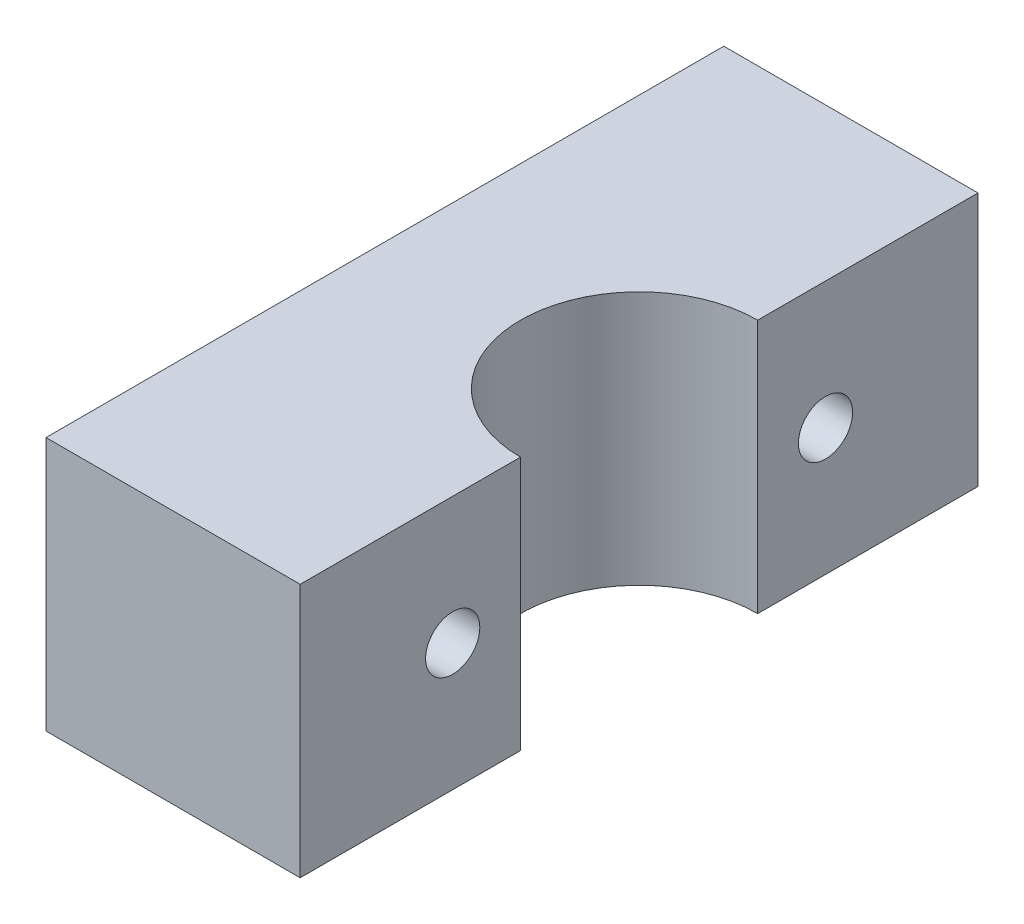
SolidWorks part; units mm, degrees
ref_plane "Спереди" through (0, 0, 0) normal (0, 0, 1) x (1, 0, 0)
ref_plane "Сверху" through (0, 0, 0) normal (0, 1, 0) x (1, 0, 0)
ref_plane "Справа" through (0, 0, 0) normal (1, 0, 0) x (0, 0, -1)
sketch "Sketch1" plane through (0, 0, 0) normal (0, 1, 0) x (1, 0, 0)
  line L0 (7.5, 20) -> (7.5, 7)
  line L1 (7.5, -20) -> (-7.5, -20)
  line L2 (7.5, -20) -> (7.5, 20) construction
  line L3 (7.5, 20) -> (-7.5, 20)
  line L4 (-7.5, -20) -> (-7.5, 20)
  line L5 (7.5, -20) -> (-7.5, 20) construction
  line L6 (7.5, 20) -> (-7.5, -20) construction
  line L7 (7.5, -7) -> (7.5, -20)
  arc A0 (7.5, 7) -> (7.5, -7) centre (7.5, 0) ccw
  point P0 (0, 0)
  dimension "D3" = 7
  dimension "D1" = 15
  dimension "D2" = 40
extrude "Boss-Extrude1" add sketch "Sketch1" along normal blind 15
sketch "Sketch4" plane through (7.5, 0, 0) normal (1, 0, 0) x (0, 0, -1)
  line L0 (20, 7.5) -> (-20, 7.5) construction
  line L1 (20, 15) -> (20, 0) construction
  line L2 (-20, 15) -> (-20, 0) construction
  circle A0 centre (11, 7.5) radius 1.6
  circle A1 centre (-11, 7.5) radius 1.6
  point P10 (0, 7.5)
  dimension "D1" = 22
  dimension "D3" = 3.2
  dimension "D2" = 11
extrude "Cut-Extrude2" cut sketch "Sketch4" against normal up to next
